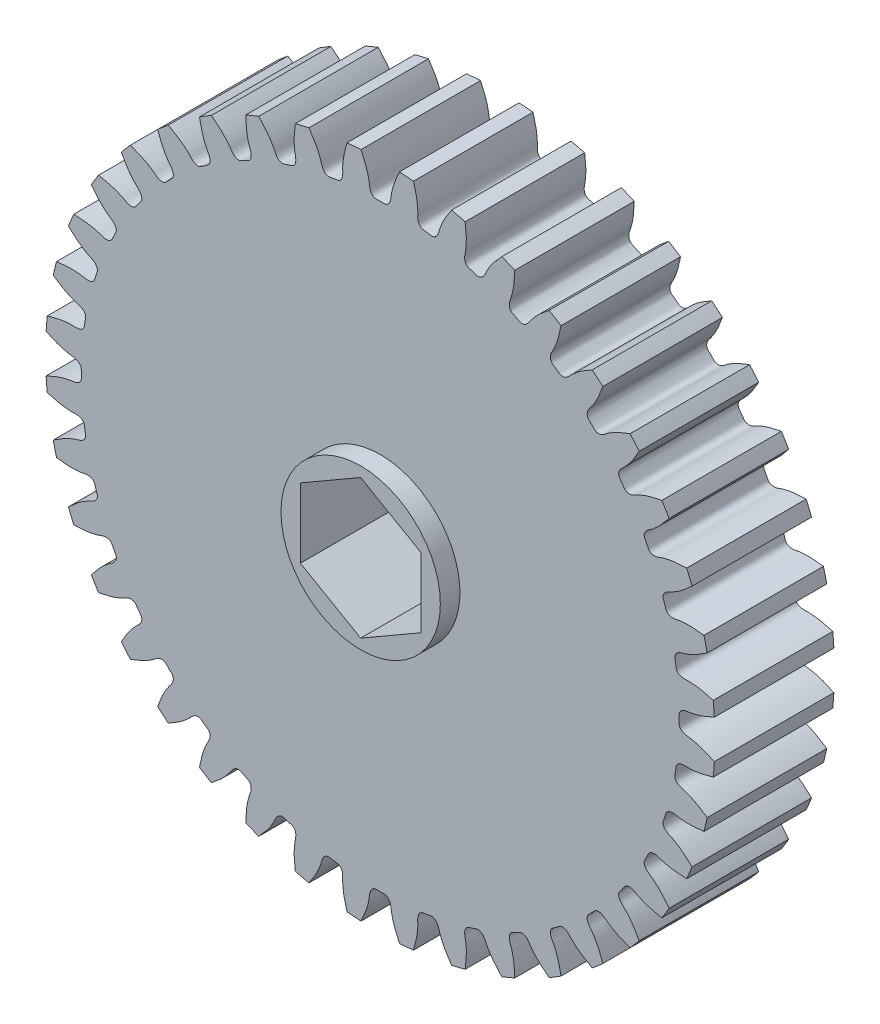
SolidWorks part; units mm, degrees
ref_plane "Front Plane" through (0, 0, 0) normal (0, 0, 1) x (1, 0, 0)
ref_plane "Top Plane" through (0, 0, 0) normal (0, 1, 0) x (1, 0, 0)
ref_plane "Right Plane" through (0, 0, 0) normal (1, 0, 0) x (0, 0, -1)
ref_plane "Plane1" through (0, 0, -4.7625) normal (0, 0, -1) x (-1, 0, 0)
sketch "Sketch1" plane through (0, 0, -4.7625) normal (0, 0, -1) x (-1, 0, 0)
  arc A0 (-25.7968, 6.7684) -> (-26.058, 5.6808) centre (0, 0) ccw
  arc A1 (-26.5381, 2.6496) -> (-26.6258, 1.5345) centre (0, 0) ccw
  arc A2 (-26.6258, -1.5345) -> (-26.5381, -2.6496) centre (0, 0) ccw
  arc A3 (-26.058, -5.6808) -> (-25.7968, -6.7684) centre (0, 0) ccw
  arc A4 (-24.8485, -9.6872) -> (-24.4204, -10.7206) centre (0, 0) ccw
  arc A5 (-23.0271, -13.4551) -> (-22.4427, -14.4088) centre (0, 0) ccw
  arc A6 (-20.6388, -16.8917) -> (-19.9124, -17.7422) centre (0, 0) ccw
  arc A7 (-17.7422, -19.9124) -> (-16.8917, -20.6388) centre (0, 0) ccw
  arc A8 (-14.4088, -22.4427) -> (-13.4551, -23.0271) centre (0, 0) ccw
  arc A9 (-10.7206, -24.4204) -> (-9.6872, -24.8485) centre (0, 0) ccw
  arc A10 (-6.7684, -25.7968) -> (-5.6808, -26.058) centre (0, 0) ccw
  arc A11 (-2.6496, -26.5381) -> (-1.5345, -26.6258) centre (0, 0) ccw
  arc A12 (1.5345, -26.6258) -> (2.6496, -26.5381) centre (0, 0) ccw
  arc A13 (5.6808, -26.058) -> (6.7684, -25.7968) centre (0, 0) ccw
  arc A14 (9.6872, -24.8485) -> (10.7206, -24.4204) centre (0, 0) ccw
  arc A15 (13.4551, -23.0271) -> (14.4088, -22.4427) centre (0, 0) ccw
  arc A16 (16.8917, -20.6388) -> (17.7422, -19.9124) centre (0, 0) ccw
  arc A17 (19.9124, -17.7422) -> (20.6388, -16.8917) centre (0, 0) ccw
  arc A18 (22.4427, -14.4088) -> (23.0271, -13.4551) centre (0, 0) ccw
  arc A19 (24.4204, -10.7206) -> (24.8485, -9.6872) centre (0, 0) ccw
  arc A20 (25.7968, -6.7684) -> (26.058, -5.6808) centre (0, 0) ccw
  arc A21 (26.5381, -2.6496) -> (26.6258, -1.5345) centre (0, 0) ccw
  arc A22 (26.6258, 1.5345) -> (26.5381, 2.6496) centre (0, 0) ccw
  arc A23 (26.058, 5.6808) -> (25.7968, 6.7684) centre (0, 0) ccw
  arc A24 (24.8485, 9.6872) -> (24.4204, 10.7206) centre (0, 0) ccw
  arc A25 (23.0271, 13.4551) -> (22.4427, 14.4088) centre (0, 0) ccw
  arc A26 (20.6388, 16.8917) -> (19.9124, 17.7422) centre (0, 0) ccw
  arc A27 (17.7422, 19.9124) -> (16.8917, 20.6388) centre (0, 0) ccw
  arc A28 (14.4088, 22.4427) -> (13.4551, 23.0271) centre (0, 0) ccw
  arc A29 (10.7206, 24.4204) -> (9.6872, 24.8485) centre (0, 0) ccw
  arc A30 (6.7684, 25.7968) -> (5.6808, 26.058) centre (0, 0) ccw
  arc A31 (2.6496, 26.5381) -> (1.5345, 26.6258) centre (0, 0) ccw
  arc A32 (-1.5345, 26.6258) -> (-2.6496, 26.5381) centre (0, 0) ccw
  arc A33 (-5.6808, 26.058) -> (-6.7684, 25.7968) centre (0, 0) ccw
  arc A34 (-9.6872, 24.8485) -> (-10.7206, 24.4204) centre (0, 0) ccw
  arc A35 (-13.4551, 23.0271) -> (-14.4088, 22.4427) centre (0, 0) ccw
  arc A36 (-16.8917, 20.6388) -> (-17.7422, 19.9124) centre (0, 0) ccw
  arc A37 (-19.9124, 17.7422) -> (-20.6388, 16.8917) centre (0, 0) ccw
  arc A38 (-22.4427, 14.4088) -> (-23.0271, 13.4551) centre (0, 0) ccw
  arc A39 (-24.4204, 10.7206) -> (-24.8485, 9.6872) centre (0, 0) ccw
  spline S0 degree 3 number of poles 87 (-25.7968, 6.7684) -> (-24.8485, 9.6872)
  spline S1 degree 3 number of poles 87 (-26.5381, 2.6496) -> (-26.058, 5.6808)
  spline S2 degree 3 number of poles 87 (-26.6258, -1.5345) -> (-26.6258, 1.5345)
  spline S3 degree 3 number of poles 87 (-26.058, -5.6808) -> (-26.5381, -2.6496)
  spline S4 degree 3 number of poles 87 (-24.8485, -9.6872) -> (-25.7968, -6.7684)
  spline S5 degree 3 number of poles 87 (-23.0271, -13.4551) -> (-24.4204, -10.7206)
  spline S6 degree 3 number of poles 87 (-20.6388, -16.8917) -> (-22.4427, -14.4088)
  spline S7 degree 3 number of poles 87 (-17.7422, -19.9124) -> (-19.9124, -17.7422)
  spline S8 degree 3 number of poles 87 (-14.4088, -22.4427) -> (-16.8917, -20.6388)
  spline S9 degree 3 number of poles 87 (-10.7206, -24.4204) -> (-13.4551, -23.0271)
  spline S10 degree 3 number of poles 87 (-6.7684, -25.7968) -> (-9.6872, -24.8485)
  spline S11 degree 3 number of poles 87 (-2.6496, -26.5381) -> (-5.6808, -26.058)
  spline S12 degree 3 number of poles 87 (1.5345, -26.6258) -> (-1.5345, -26.6258)
  spline S13 degree 3 number of poles 87 (5.6808, -26.058) -> (2.6496, -26.5381)
  spline S14 degree 3 number of poles 87 (9.6872, -24.8485) -> (6.7684, -25.7968)
  spline S15 degree 3 number of poles 87 (13.4551, -23.0271) -> (10.7206, -24.4204)
  spline S16 degree 3 number of poles 87 (16.8917, -20.6388) -> (14.4088, -22.4427)
  spline S17 degree 3 number of poles 87 (19.9124, -17.7422) -> (17.7422, -19.9124)
  spline S18 degree 3 number of poles 87 (22.4427, -14.4088) -> (20.6388, -16.8917)
  spline S19 degree 3 number of poles 87 (24.4204, -10.7206) -> (23.0271, -13.4551)
  spline S20 degree 3 number of poles 87 (25.7968, -6.7684) -> (24.8485, -9.6872)
  spline S21 degree 3 number of poles 87 (26.5381, -2.6496) -> (26.058, -5.6808)
  spline S22 degree 3 number of poles 87 (26.6258, 1.5345) -> (26.6258, -1.5345)
  spline S23 degree 3 number of poles 87 (26.058, 5.6808) -> (26.5381, 2.6496)
  spline S24 degree 3 number of poles 87 (24.8485, 9.6872) -> (25.7968, 6.7684)
  spline S25 degree 3 number of poles 87 (23.0271, 13.4551) -> (24.4204, 10.7206)
  spline S26 degree 3 number of poles 87 (20.6388, 16.8917) -> (22.4427, 14.4088)
  spline S27 degree 3 number of poles 87 (17.7422, 19.9124) -> (19.9124, 17.7422)
  spline S28 degree 3 number of poles 87 (14.4088, 22.4427) -> (16.8917, 20.6388)
  spline S29 degree 3 number of poles 87 (10.7206, 24.4204) -> (13.4551, 23.0271)
  spline S30 degree 3 number of poles 87 (6.7684, 25.7968) -> (9.6872, 24.8485)
  spline S31 degree 3 number of poles 87 (2.6496, 26.5381) -> (5.6808, 26.058)
  spline S32 degree 3 number of poles 87 (-1.5345, 26.6258) -> (1.5345, 26.6258)
  spline S33 degree 3 number of poles 87 (-5.6808, 26.058) -> (-2.6496, 26.5381)
  spline S34 degree 3 number of poles 87 (-9.6872, 24.8485) -> (-6.7684, 25.7968)
  spline S35 degree 3 number of poles 87 (-13.4551, 23.0271) -> (-10.7206, 24.4204)
  spline S36 degree 3 number of poles 87 (-16.8917, 20.6388) -> (-14.4088, 22.4427)
  spline S37 degree 3 number of poles 87 (-19.9124, 17.7422) -> (-17.7422, 19.9124)
  spline S38 degree 3 number of poles 87 (-22.4427, 14.4088) -> (-20.6388, 16.8917)
  spline S39 degree 3 number of poles 87 (-24.4204, 10.7206) -> (-23.0271, 13.4551)
extrude "Boss-Extrude1" add sketch "Sketch1" against normal blind 9.525
sketch "Sketch2" plane through (0, 0, -4.7625) normal (0, 0, -1) x (-1, 0, 0)
  circle A0 centre (0, 0) radius 6.35
extrude "Boss-Extrude2" add sketch "Sketch2" along normal blind 1.5621
sketch "Sketch3" plane through (0, 0, 4.7625) normal (0, 0, 1) x (1, 0, 0)
  circle A0 centre (0, 0) radius 6.35
extrude "Boss-Extrude3" add sketch "Sketch3" along normal blind 1.5621
sketch "Sketch4" plane through (0, 0, 6.3246) normal (0, 0, 1) x (1, 0, 0)
  line L0 (4.8006, -2.7716) -> (4.8006, 2.7716)
  line L1 (4.8006, 2.7716) -> (0, 5.5433)
  line L2 (0, 5.5433) -> (-4.8006, 2.7716)
  line L3 (-4.8006, 2.7716) -> (-4.8006, -2.7716)
  line L4 (-4.8006, -2.7716) -> (0, -5.5433)
  line L5 (0, -5.5433) -> (4.8006, -2.7716)
extrude "Cut-Extrude1" cut sketch "Sketch4" against normal through all
